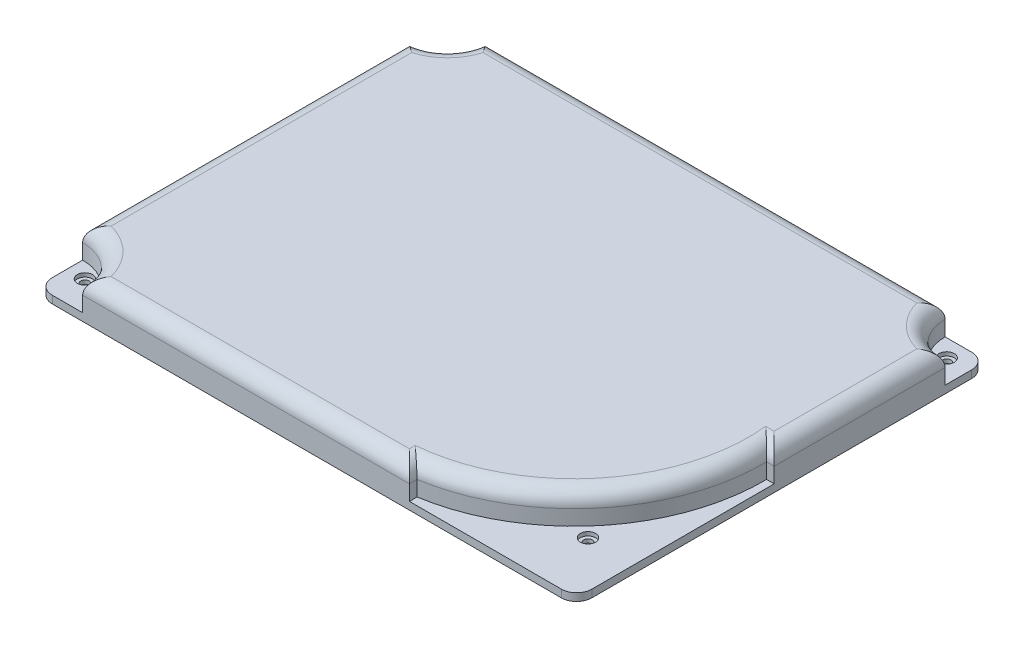
SolidWorks part; units mm, degrees
material "1060 Alloy for HDD "
ref_plane "Front Plane" through (0, 0, 0) normal (0, 0, 1) x (1, 0, 0)
ref_plane "Top Plane" through (0, 0, 0) normal (0, 1, 0) x (1, 0, 0)
ref_plane "Right Plane" through (0, 0, 0) normal (1, 0, 0) x (0, 0, -1)
sketch "Sketch1" plane through (0, 0, 0) normal (0, 1, 0) x (1, 0, 0)
  line L1 (-35.5, -27) -> (35.5, -27)
  line L2 (-35.5, -27) -> (-35.5, 27)
  line L3 (-35.5, 27) -> (35.5, 27)
  line L4 (35.5, -27) -> (35.5, 27)
  line L5 (-35.5, -27) -> (35.5, 27) construction
  line L6 (-35.5, 27) -> (35.5, -27) construction
  point P0 (0, 0)
  dimension "D1" = 71
  dimension "D2" = 54
extrude "Boss-Extrude1" add sketch "Sketch1" along normal blind 5
hole_wizard "M1.4x0.3 Tapped Hole1" positions "Sketch2" profile "Sketch3" tap size "M1.4x0.3" standard "ANSI Metric" end condition through all
sketch "Sketch2" plane through (0, 5, 0) normal (0, 1, 0) x (1, 0, 0)
  line L0 (-35.5, 27) -> (-35.5, -27) construction
  line L1 (35.5, 27) -> (-35.5, 27) construction
  line L2 (-35.5, -27) -> (35.5, -27) construction
  line L3 (35.5, -27) -> (35.5, 27) construction
  point P0 (-33.2, 24.7)
  point P2 (32.5, 24.7)
  point P4 (-33.2, -23)
  point P6 (29.4, -19.4)
  dimension "D1" = 2.3
  dimension "D2" = 2.3
  dimension "D3" = 4
  dimension "D4" = 2.3
  dimension "D5" = 7.6
  dimension "D6" = 6.1
  dimension "D7" = 3
  dimension "D8" = 2.3
sketch "Sketch3" plane through (-33.2, 5, -24.7) normal (1, 0, 0) x (0, 0, 1)
  line L0 (0, 0) -> (0, 5)
  line L1 (0, 5) -> (0.55, 5)
  line L2 (0.55, 5) -> (0.55, 0.175)
  line L3 (0.55, 0.175) -> (0.725, 0)
  line L5 (0.725, 0) -> (0, 0)
  line L6 (-0.55, 0.175) -> (-0.725, 0) construction
  line L11 (0, -6.35) -> (0, 107.95) construction
  dimension "Thru Tap Drill Dia." = 1.1
  dimension "Thru Tap Drill Depth" = 5
  dimension "Near C'Sink Dia." = 1.45
  dimension "Near C'Sink Angle" = 90
cosmetic thread "Hole Thread1" parameters "D2"=1.4
cosmetic thread "Hole Thread2" parameters "D2"=1.4
cosmetic thread "Hole Thread3" parameters "D2"=1.4
cosmetic thread "Hole Thread4" parameters "D2"=1.4
sketch "Sketch4" plane through (0, 0, 0) normal (0, -1, 0) x (1, 0, 0)
  line L0 (-35.5, -27) -> (-35.5, 27) construction
  line L1 (35.5, -27) -> (-35.5, -27) construction
  line L2 (-7.7481, 19) -> (-33.5, 19)
  line L4 (-6.5, -20) -> (-33.5, -20)
  line L5 (-33.5, 19) -> (-33.5, -20)
  line L6 (-35.5, 27) -> (35.5, 27) construction
  arc A0 (-6.5, -20) -> (-7.7481, 19) centre (8.5, 0) ccw
  dimension "D2" = 50
  dimension "D1" = 44
  dimension "D3" = 2
  dimension "D4" = 7
  dimension "D5" = 8
extrude "Cut-Extrude1" cut sketch "Sketch4" against normal blind 4
sketch "Sketch5" plane through (0, 5, 0) normal (0, 1, 0) x (1, 0, 0)
  line L1 (34.5, -1) -> (35.5, -1)
  line L2 (35.5, -27) -> (35.5, 27) construction
  line L3 (35.5, -1) -> (35.5, -27)
  line L5 (-35.5, 27) -> (-35.5, -27) construction
  line L6 (13.5, -26) -> (13.5, -27)
  line L7 (13.5, -27) -> (35.5, -27)
  line L8 (35.5, -27) -> (35.5, 27) construction
  line L9 (-35.5, -27) -> (35.5, -27) construction
  circle A0 centre (-35.5, -27) radius 6
  circle A1 centre (-35.5, 27) radius 5
  circle A3 centre (35.5, 27) radius 5.5
  arc A4 (34.5, -1) -> (13.5, -26) centre (9.5021, -1.3217) cw
  dimension "D1" = 10
  dimension "D2" = 11
  dimension "D3" = 12
  dimension "D4" = 25
  dimension "D5" = 1
  dimension "D6" = 1
  dimension "D7" = 22
  dimension "D8" = 26
extrude "Cut-Extrude2" cut sketch "Sketch5" against normal blind 4
fillet "Fillet1" radius 2 4 edges at (-35.5, 0.5, -27) (35.5, 0.5, -27) (35.5, 0.5, 27) (-35.5, 0.5, 27)
fillet "Fillet2" radius 2 10 edges at (31.6109, 5, -23.1109) (35.5, 5, -10.25) (35, 5, 1) (13.5, 5, 26.5) (28.6447, 5, 17.4015) (-8, 5, 27) (-31.2574, 5, 22.7574) (-35.5, 5, -0.5) (-31.9645, 5, -23.4645) (-0.25, 5, -27)
sketch "Sketch6" plane through (0, 1, 0) normal (0, 1, 0) x (1, 0, 0)
  circle A0 centre (-33.2, 24.7) radius 1
  circle A1 centre (32.5, 24.7) radius 1
  circle A2 centre (29.4, -19.4) radius 1
  circle A3 centre (-33.2, -23) radius 1
  dimension "D1" = 2
  dimension "D2" = 2
  dimension "D3" = 2
  dimension "D4" = 2
extrude "Cut-Extrude3" cut sketch "Sketch6" against normal blind 0.5
